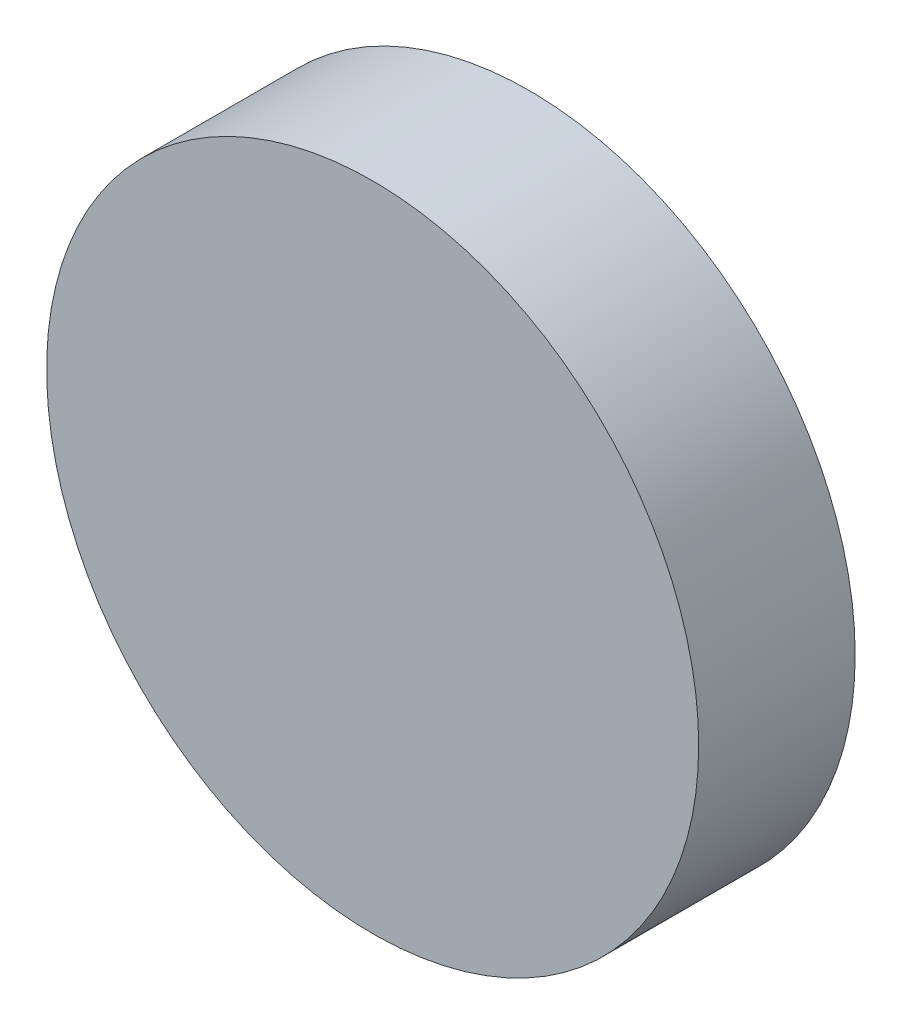
SolidWorks part; units mm, degrees
ref_plane "前视基准面" through (0, 0, 0) normal (0, 0, 1) x (1, 0, 0)
ref_plane "上视基准面" through (0, 0, 0) normal (0, 1, 0) x (1, 0, 0)
ref_plane "右视基准面" through (0, 0, 0) normal (1, 0, 0) x (0, 0, -1)
sketch "草图1" plane through (0, 0, 0) normal (0, 0, 1) x (1, 0, 0)
  circle A0 centre (0, 0) radius 12.5
  dimension "D1" = 25
extrude "凸台-拉伸1" add sketch "草图1" along normal blind 6 contours A0
